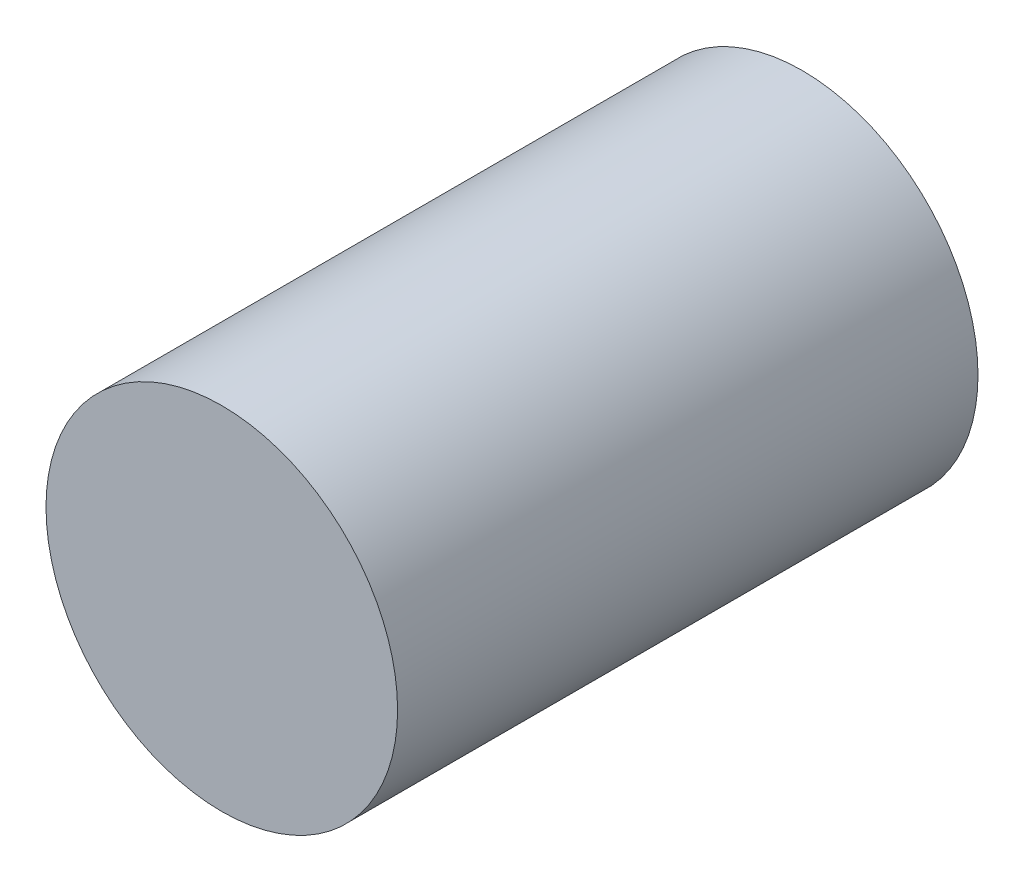
SolidWorks part; units mm, degrees
ref_plane "Front Plane" through (0, 0, 0) normal (0, 0, 1) x (1, 0, 0)
ref_plane "Top Plane" through (0, 0, 0) normal (0, 1, 0) x (1, 0, 0)
ref_plane "Right Plane" through (0, 0, 0) normal (1, 0, 0) x (0, 0, -1)
sketch "Sketch1" plane through (0, 0, 0) normal (0, 0, 1) x (1, 0, 0)
  circle A0 centre (0, 0) radius 0.9995
  dimension "D1" = 1.999
extrude "Boss-Extrude1" add sketch "Sketch1" along normal blind 3.3
